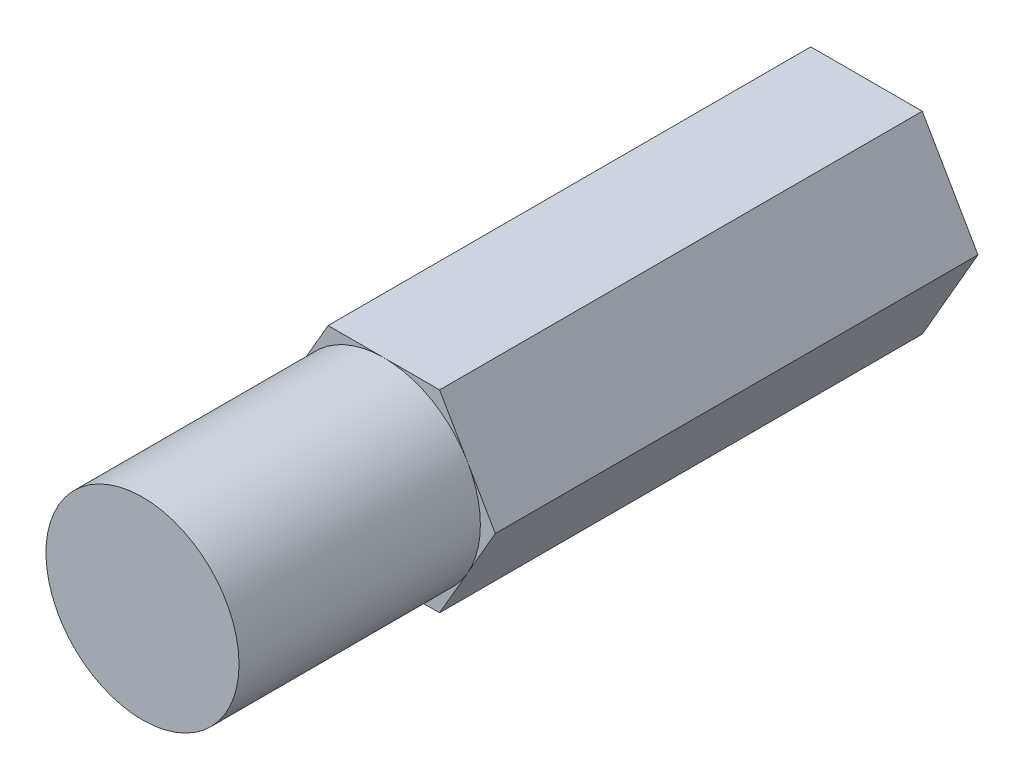
SolidWorks part; units mm, degrees
ref_plane "Front Plane" through (0, 0, 0) normal (0, 0, 1) x (1, 0, 0)
ref_plane "Top Plane" through (0, 0, 0) normal (0, 1, 0) x (1, 0, 0)
ref_plane "Right Plane" through (0, 0, 0) normal (1, 0, 0) x (0, 0, -1)
sketch "Sketch1" plane through (0, 0, 0) normal (0, 0, 1) x (1, 0, 0)
  line L1 (-1.1547, -2) -> (1.1547, -2)
  line L2 (1.1547, -2) -> (2.3094, 0)
  line L3 (2.3094, 0) -> (1.1547, 2)
  line L4 (1.1547, 2) -> (-1.1547, 2)
  line L5 (-1.1547, 2) -> (-2.3094, 0)
  line L6 (-2.3094, 0) -> (-1.1547, -2)
  circle A0 centre (0, 0) radius 2 construction
  dimension "D1" = 4
extrude "Boss-Extrude1" add sketch "Sketch1" along normal blind 10
sketch "Sketch2" plane through (0, 0, 10) normal (0, 0, 1) x (1, 0, 0)
  circle A0 centre (0, 0) radius 2
  dimension "D1" = 4
extrude "Boss-Extrude2" add sketch "Sketch2" along normal blind 5
